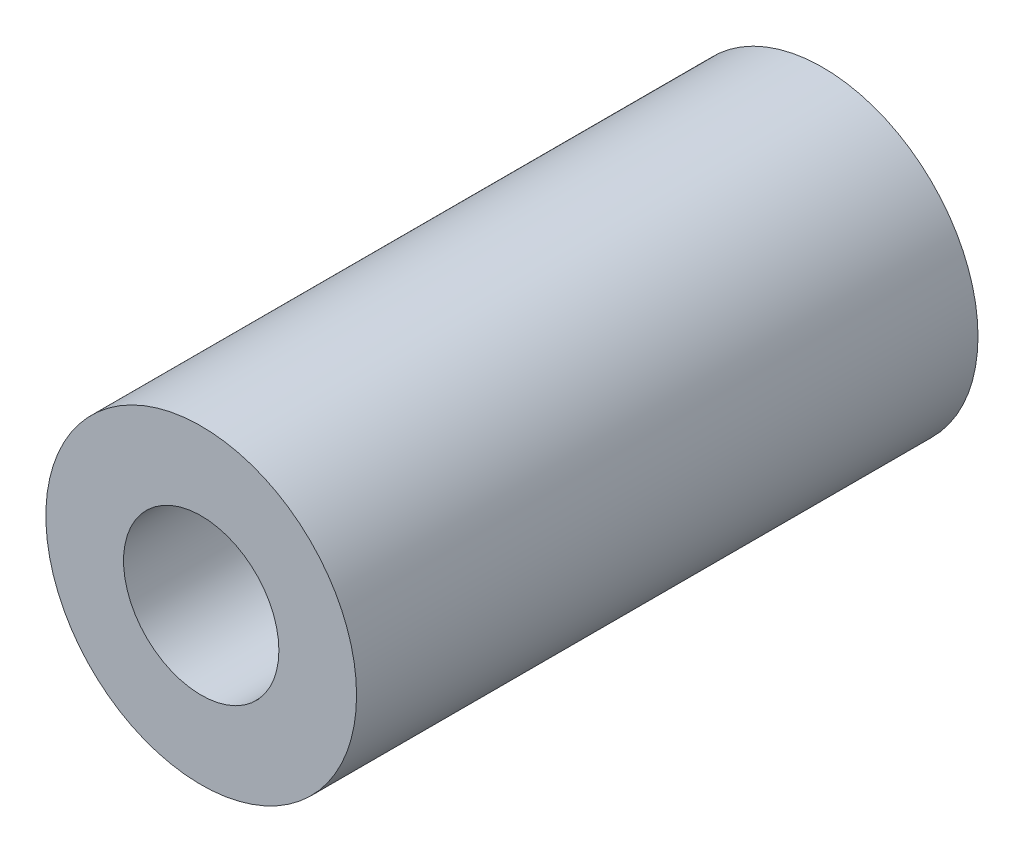
SolidWorks part; units mm, degrees
material "Rubber"
ref_plane "Front Plane" through (0, 0, 0) normal (0, 0, 1) x (1, 0, 0)
ref_plane "Top Plane" through (0, 0, 0) normal (0, 1, 0) x (1, 0, 0)
ref_plane "Right Plane" through (0, 0, 0) normal (1, 0, 0) x (0, 0, -1)
sketch "Sketch1" plane through (0, 0, 0) normal (0, 0, 1) x (1, 0, 0)
  circle A0 centre (0, 0) radius 12.7
  circle A1 centre (0, 0) radius 6.35
  dimension "D1" = 25.4
  dimension "D2" = 12.7
extrude "Boss-Extrude1" add sketch "Sketch1" along normal blind 50.8
